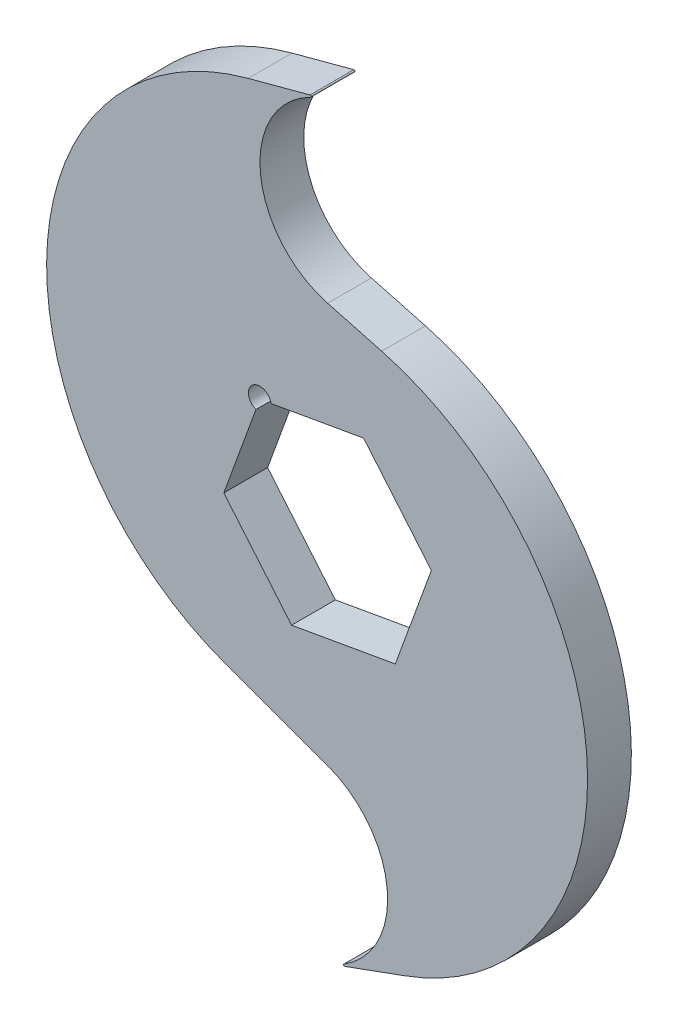
SolidWorks part; units mm, degrees
ref_plane "Front Plane" through (0, 0, 0) normal (0, 0, 1) x (1, 0, 0)
ref_plane "Top Plane" through (0, 0, 0) normal (0, 1, 0) x (1, 0, 0)
ref_plane "Right Plane" through (0, 0, 0) normal (1, 0, 0) x (0, 0, -1)
sketch "Sketch1" plane through (0, 0, 0) normal (0, 0, 1) x (1, 0, 0)
  line L0 (0, 52.07) -> (-11.0405, 49.1117)
  line L1 (0, 52.07) -> (0, 0) construction
  line L2 (0, -52.07) -> (10.7407, -48.1607)
  line L3 (0, 0) -> (0, -52.07) construction
  line L5 (-9.4263, 11.2338) -> (-14.4419, -2.5465)
  line L6 (-14.4419, -2.5465) -> (-5.0156, -13.7803)
  line L7 (-5.0156, -13.7803) -> (9.4263, -11.2338)
  line L8 (9.4263, -11.2338) -> (14.4419, 2.5465)
  line L9 (14.4419, 2.5465) -> (5.0156, 13.7803)
  line L10 (5.0156, 13.7803) -> (-9.4263, 11.2338)
  line L11 (0, 27.5355) -> (7.5237, 25.5195)
  line L12 (0, -28.2018) -> (-14.1906, -23.0368)
  circle A0 centre (0, 0) radius 52.07 construction
  arc A1 (0, 52.07) -> (0, 27.5355) centre (3.287, 39.8027) ccw
  arc A3 (0, -52.07) -> (0, -28.2018) centre (-4.3437, -40.1359) ccw
  arc A4 (10.7407, -48.1607) -> (7.5237, 25.5195) centre (-2.4834, -11.8278) ccw
  arc A5 (-11.0405, 49.1117) -> (-14.1906, -23.0368) centre (-1.2414, 12.5408) ccw
  circle A6 centre (0, 0) radius 12.7 construction
  circle A7 centre (-9.4263, 11.2338) radius 1.5875
  dimension "D4" = 70
  dimension "D5" = 25.4
  dimension "D1" = 104.14
  dimension "D6" = 12.7
  dimension "D8" = 3.175
  dimension "D2" = 11.43
  dimension "D3" = 75
  dimension "D7" = 40
extrude "Boss-Extrude1" add sketch "Sketch1" along normal mid plane 6.096 contours L0 A5 L12 A3 L2 A4 L11 A1 A7 L10 L9 L8 L7 L6 L5
fillet "Fillet1" radius 0.127 2 edges at (0, 52.07, 0) (0, -52.07, 0)
